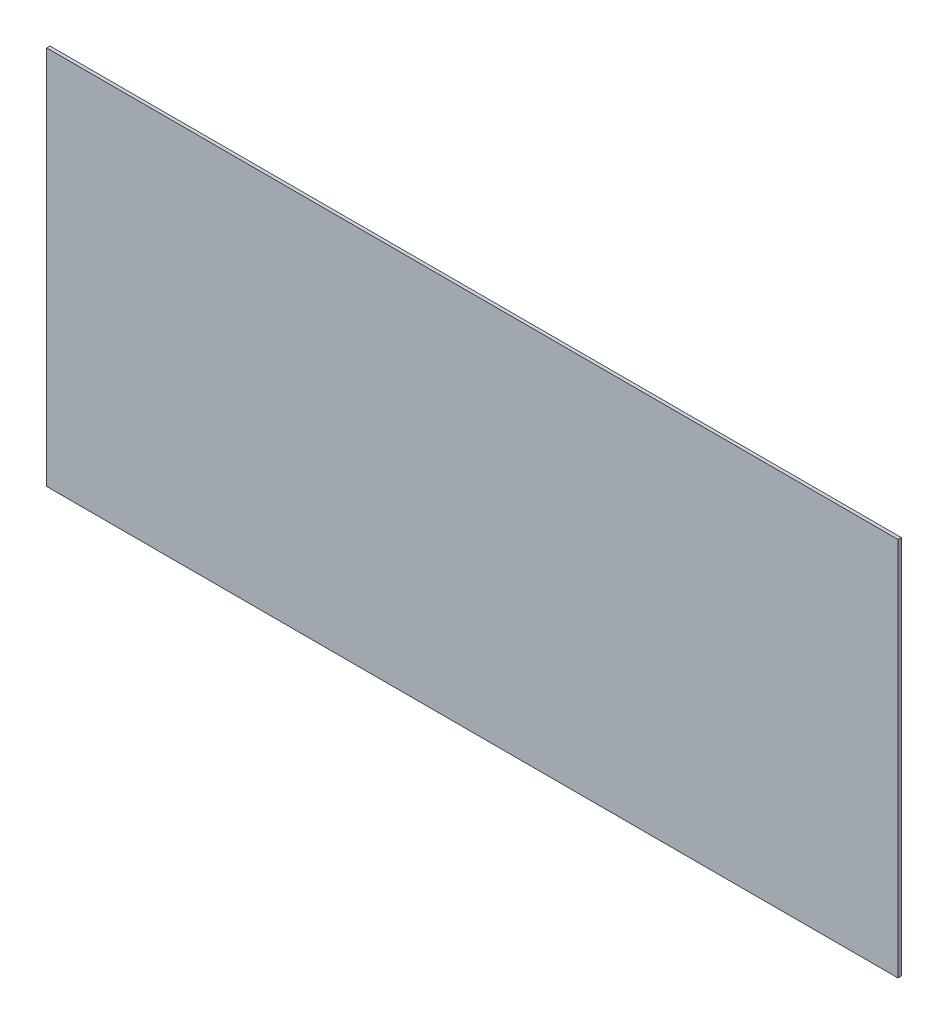
SolidWorks part; units mm, degrees
ref_plane "Plan de face" through (0, 0, 0) normal (0, 0, 1) x (1, 0, 0)
ref_plane "Plan de dessus" through (0, 0, 0) normal (0, 1, 0) x (1, 0, 0)
ref_plane "Plan de droite" through (0, 0, 0) normal (1, 0, 0) x (0, 0, -1)
sketch "Esquisse1" plane through (0, 0, 0) normal (0, 0, 1) x (1, 0, 0)
  line L1 (-13, -5.8) -> (13, -5.8)
  line L2 (-13, -5.8) -> (-13, 5.8)
  line L3 (-13, 5.8) -> (13, 5.8)
  line L4 (13, -5.8) -> (13, 5.8)
  line L5 (-13, -5.8) -> (13, 5.8) construction
  line L6 (-13, 5.8) -> (13, -5.8) construction
  point P0 (0, 0)
  dimension "D1" = 26
  dimension "D2" = 11.6
extrude "Boss.-Extru.1" add sketch "Esquisse1" along normal blind 0.1
